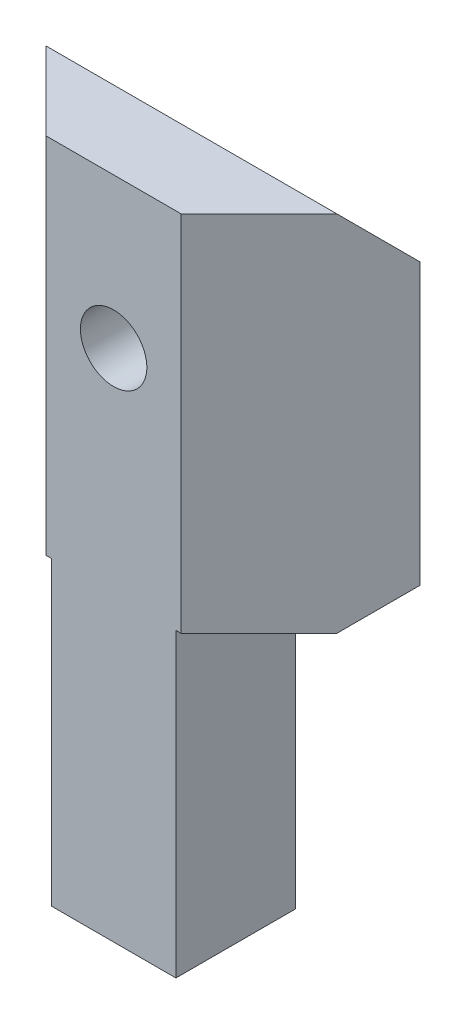
SolidWorks part; units mm, degrees
ref_plane "Front Plane" through (0, 0, 0) normal (0, 0, 1) x (1, 0, 0)
ref_plane "Top Plane" through (0, 0, 0) normal (0, 1, 0) x (1, 0, 0)
ref_plane "Right Plane" through (0, 0, 0) normal (1, 0, 0) x (0, 0, -1)
sketch "Sketch1" plane through (0, 0, 0) normal (0, 1, 0) x (1, 0, 0)
  line L0 (-16.8006, 6.8049) -> (1.1994, 6.8049)
  line L1 (-10.8006, 0.8049) -> (-4.8006, 0.8049)
  line L2 (-10.8006, 0.8049) -> (-16.8006, 6.8049)
  line L3 (1.1994, 6.8049) -> (-4.8006, 0.8049)
  line L5 (-16.8006, 0.8049) -> (1.1994, 0.8049) construction
  dimension "D1" = 45
  dimension "D3" = 6
  dimension "D4" = 45
  dimension "D2" = 6
extrude "Boss-Extrude1" add sketch "Sketch1" along normal blind 32
chamfer "Chamfer1" distance 2 angle 45 1 edges at (-7.8006, 32, -6.8049)
sketch "Sketch2" plane through (0, 0, 0) normal (0, -1, 0) x (1, 0, 0)
  line L0 (-4.8006, -0.8049) -> (-4.8006, -6.8049)
  line L1 (1.1994, -6.8049) -> (-16.8006, -6.8049) construction
  line L2 (-4.8006, -6.8049) -> (1.1994, -6.8049)
  line L3 (1.1994, -6.8049) -> (-4.8006, -0.8049)
  line L4 (-10.8006, -0.8049) -> (-10.8006, -6.8049)
  line L5 (-10.8006, -6.8049) -> (-16.8006, -6.8049)
  line L6 (-16.8006, -6.8049) -> (-10.8006, -0.8049)
extrude "Cut-Extrude1" cut sketch "Sketch2" against normal blind 14.5
chamfer "Chamfer2" distance 2 angle 45 2 edges at (-13.8006, 14.5, -6.8049) (-1.8006, 14.5, -6.8049)
sketch "Sketch3" plane through (0, 0, 0) normal (0, -1, 0) x (1, 0, 0)
  line L0 (-7.8006, -6.8049) -> (-7.8006, -0.8049) construction
  line L1 (-4.8006, -6.8049) -> (-10.8006, -6.8049) construction
  line L2 (-10.8006, -0.8049) -> (-4.8006, -0.8049) construction
  circle A0 centre (-7.8006, -3.8049) radius 1.625
  dimension "D1" = 3.25
extrude "Cut-Extrude2" cut sketch "Sketch3" against normal blind 4
sketch "Sketch4" plane through (0, 0, -6.8049) normal (0, 0, -1) x (-1, 0, 0)
  line L0 (7.8006, 30) -> (7.8006, 0) construction
  line L1 (16.8006, 30) -> (-1.1994, 30) construction
  line L2 (4.8006, 0) -> (10.8006, 0) construction
  circle A0 centre (7.8006, 24.7693) radius 1.6
  dimension "D1" = 3.2
  dimension "D2" = 7.2307
extrude "Cut-Extrude3" cut sketch "Sketch4" against normal through all
sketch "Sketch5" plane through (0, 0, -6.8049) normal (0, 0, -1) x (-1, 0, 0)
  circle A0 centre (7.8006, 24.7693) radius 2.875
  dimension "D1" = 5.75
extrude "Cut-Extrude4" cut sketch "Sketch5" against normal blind 2.5
sketch "Sketch6" plane through (0, 0, -0.8049) normal (0, 0, 1) x (1, 0, 0)
  line L1 (-2.3801, 0) -> (-12.3311, 0)
  line L3 (-12.3311, 32) -> (-2.3801, 32)
  line L4 (-2.3801, 32) -> (-2.3801, 0)
  line L5 (-12.3311, 0) -> (-12.3311, 32)
extrude "Cut-Extrude5" cut sketch "Sketch6" against normal blind 0.25
